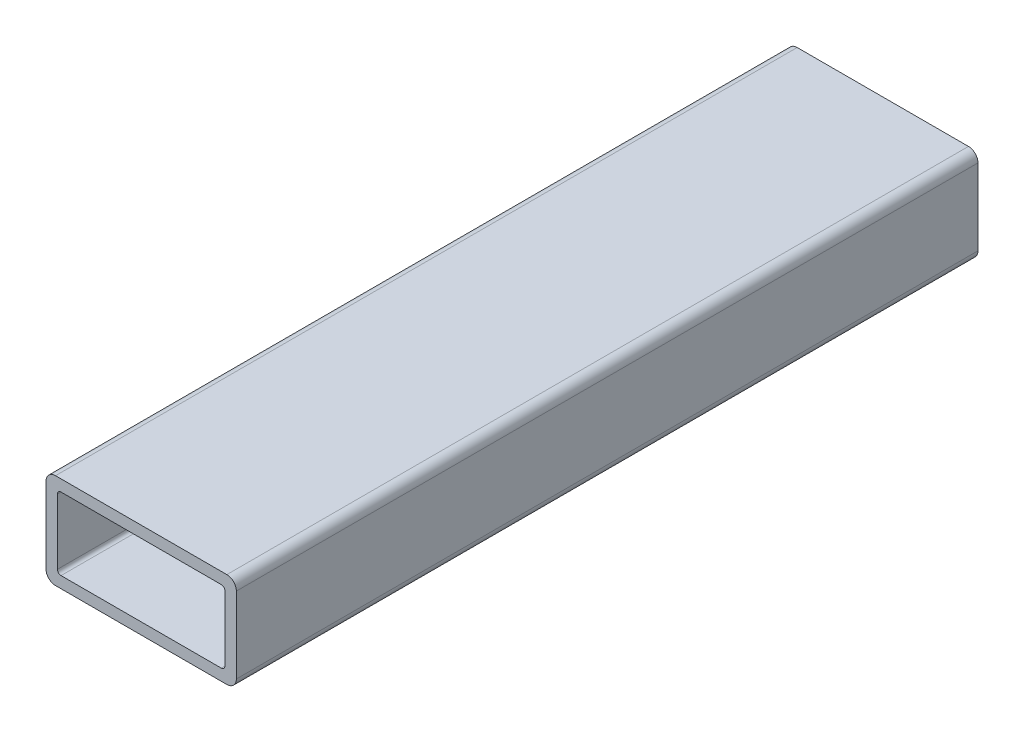
SolidWorks part; units mm, degrees
ref_plane "Front" through (0, 0, 0) normal (0, 0, 1) x (1, 0, 0)
ref_plane "Top" through (0, 0, 0) normal (0, 1, 0) x (1, 0, 0)
ref_plane "Right" through (0, 0, 0) normal (1, 0, 0) x (0, 0, -1)
sketch "Sketch1" plane through (0, 0, 0) normal (0, 0, 1) x (1, 0, 0)
  line L0 (-22.352, 0) -> (-25.4, 0) construction
  line L1 (22.86, -12.7) -> (-22.86, -12.7)
  line L2 (25.4, -10.16) -> (25.4, 10.16)
  line L3 (22.86, 12.7) -> (-22.86, 12.7)
  line L4 (-25.4, -10.16) -> (-25.4, 10.16)
  line L5 (25.4, -12.7) -> (-25.4, 12.7) construction
  line L6 (25.4, 12.7) -> (-25.4, -12.7) construction
  line L7 (21.3868, 9.652) -> (-21.3868, 9.652)
  line L8 (22.352, 8.6868) -> (22.352, -8.6868)
  line L9 (21.3868, -9.652) -> (-21.3868, -9.652)
  line L10 (-22.352, 8.6868) -> (-22.352, -8.6868)
  line L11 (22.352, 9.652) -> (-22.352, -9.652) construction
  line L12 (22.352, -9.652) -> (-22.352, 9.652) construction
  line L13 (0, -9.652) -> (0, -12.7) construction
  line L14 (22.352, -8.6868) -> (22.352, -12.7) construction
  line L16 (22.352, -12.7) -> (25.4, -12.7) construction
  arc A0 (-21.3868, -9.652) -> (-22.352, -8.6868) centre (-21.3868, -8.6868) cw
  arc A1 (22.352, -8.6868) -> (21.3868, -9.652) centre (21.3868, -8.6868) cw
  arc A2 (21.3868, 9.652) -> (22.352, 8.6868) centre (21.3868, 8.6868) cw
  arc A3 (-21.3868, 9.652) -> (-22.352, 8.6868) centre (-21.3868, 8.6868) ccw
  arc A4 (22.86, -12.7) -> (25.4, -10.16) centre (22.86, -10.16) ccw
  arc A5 (25.4, 10.16) -> (22.86, 12.7) centre (22.86, 10.16) ccw
  arc A6 (-22.86, 12.7) -> (-25.4, 10.16) centre (-22.86, 10.16) ccw
  arc A7 (-22.86, -12.7) -> (-25.4, -10.16) centre (-22.86, -10.16) cw
  point P0 (0, 0)
  point P6 (0, 0)
  dimension "D2" = 0.9652
  dimension "D3" = 2.54
sketch "Sketch2" plane through (0, 0, 0) normal (1, 0, 0) x (0, 0, -1)
  line L0 (-152.4, 0) -> (152.4, 0) construction
  dimension "Length" = 304.8
ref_plane "Plane1" through (25.4, 0, 0) normal (1, 0, 0) x (0, 0, -1)
sketch "Sketch5" plane through (25.4, 0, 0) normal (1, 0, 0) x (0, 0, -1)
  line L0 (-152.4, 12.7) -> (-152.4, -12.7) construction
  line L1 (152.4, 12.7) -> (152.4, -12.7) construction
sketch "Sketch4" plane through (0, 0, 0) normal (0, 0, 1) x (1, 0, 0)
  line L0 (25.4, -10.16) -> (25.4, 10.16) construction
  line L1 (22.86, 12.7) -> (-22.86, 12.7) construction
  line L2 (-25.4, -10.16) -> (-25.4, 10.16) construction
  line L3 (22.86, -12.7) -> (-22.86, -12.7) construction
  line L4 (22.352, 8.6868) -> (22.352, -8.6868) construction
  line L5 (21.3868, -9.652) -> (-21.3868, -9.652) construction
  line L6 (-22.352, 8.6868) -> (-22.352, -8.6868) construction
  line L7 (21.3868, 9.652) -> (-21.3868, 9.652) construction
  line L8 (25.4, -10.16) -> (25.4, 10.16)
  line L9 (22.86, 12.7) -> (-22.86, 12.7)
  line L10 (-25.4, -10.16) -> (-25.4, 10.16)
  line L11 (22.86, -12.7) -> (-22.86, -12.7)
  line L12 (22.352, 8.6868) -> (22.352, -8.6868)
  line L13 (21.3868, -9.652) -> (-21.3868, -9.652)
  line L14 (-22.352, 8.6868) -> (-22.352, -8.6868)
  line L15 (21.3868, 9.652) -> (-21.3868, 9.652)
  arc A0 (25.4, 10.16) -> (22.86, 12.7) centre (22.86, 10.16) ccw construction
  arc A1 (-22.86, 12.7) -> (-25.4, 10.16) centre (-22.86, 10.16) ccw construction
  arc A2 (-25.4, -10.16) -> (-22.86, -12.7) centre (-22.86, -10.16) ccw construction
  arc A3 (22.86, -12.7) -> (25.4, -10.16) centre (22.86, -10.16) ccw construction
  arc A4 (21.3868, -9.652) -> (22.352, -8.6868) centre (21.3868, -8.6868) ccw construction
  arc A5 (-22.352, -8.6868) -> (-21.3868, -9.652) centre (-21.3868, -8.6868) ccw construction
  arc A6 (-21.3868, 9.652) -> (-22.352, 8.6868) centre (-21.3868, 8.6868) ccw construction
  arc A7 (22.352, 8.6868) -> (21.3868, 9.652) centre (21.3868, 8.6868) ccw construction
  arc A8 (25.4, 10.16) -> (22.86, 12.7) centre (22.86, 10.16) ccw
  arc A9 (-22.86, 12.7) -> (-25.4, 10.16) centre (-22.86, 10.16) ccw
  arc A10 (-25.4, -10.16) -> (-22.86, -12.7) centre (-22.86, -10.16) ccw
  arc A11 (22.86, -12.7) -> (25.4, -10.16) centre (22.86, -10.16) ccw
  arc A12 (21.3868, -9.652) -> (22.352, -8.6868) centre (21.3868, -8.6868) ccw
  arc A13 (-22.352, -8.6868) -> (-21.3868, -9.652) centre (-21.3868, -8.6868) ccw
  arc A14 (-21.3868, 9.652) -> (-22.352, 8.6868) centre (-21.3868, 8.6868) ccw
  arc A15 (22.352, 8.6868) -> (21.3868, 9.652) centre (21.3868, 8.6868) ccw
extrude "Boss-Extrude1" add sketch "Sketch4" along normal blind 197.9193
equation "\"D3@Sketch1\"=\"Outside Width@Sketch1\"*.05"
equation "\"D2@Sketch1\"=\"D1@Sketch1\"*.05"
